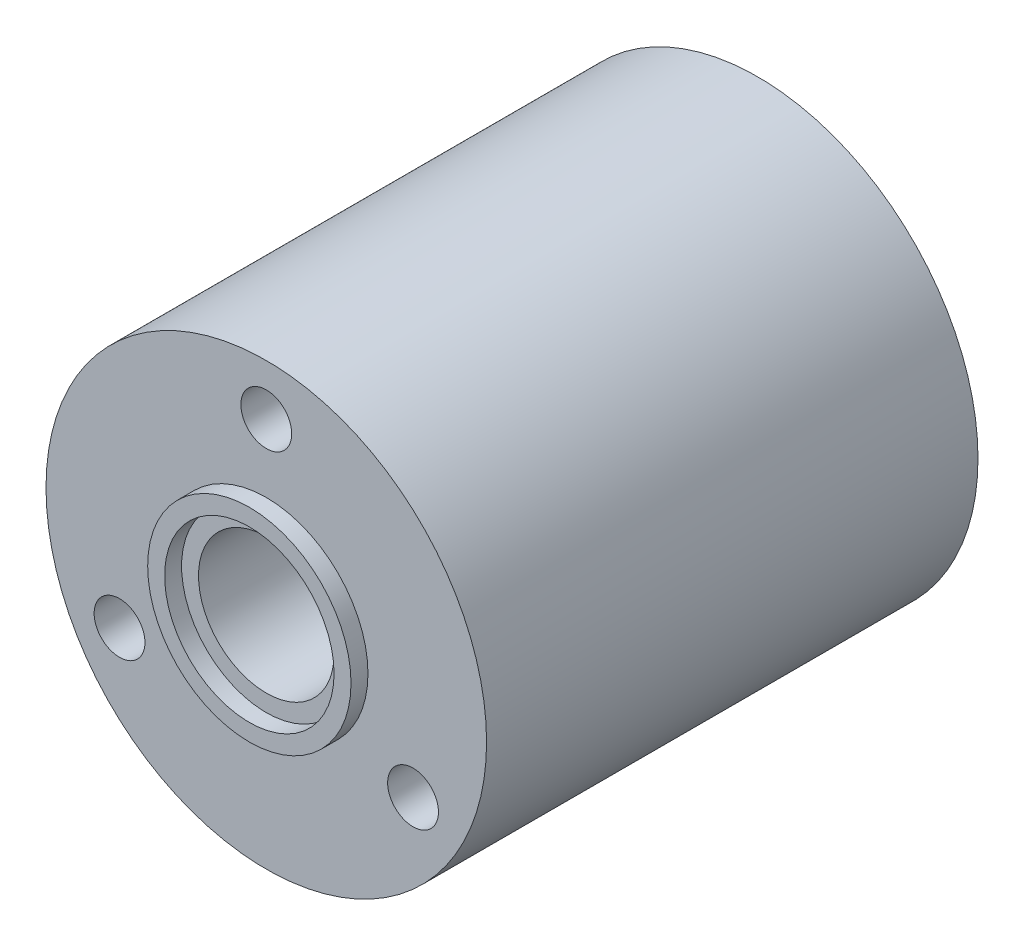
SolidWorks part; units mm, degrees
ref_plane "Front Plane" through (0, 0, 0) normal (0, 0, 1) x (1, 0, 0)
ref_plane "Top Plane" through (0, 0, 0) normal (0, 1, 0) x (1, 0, 0)
ref_plane "Right Plane" through (0, 0, 0) normal (1, 0, 0) x (0, 0, -1)
sketch "Sketch1" plane through (0, 0, 0) normal (0, 0, 1) x (1, 0, 0)
  circle A0 centre (0, 0) radius 5
  circle A1 centre (0, 0) radius 13
  dimension "D1" = 10
  dimension "D2" = 26
extrude "Boss-Extrude1" add sketch "Sketch1" along normal blind 29
sketch "Sketch2" plane through (0, 0, 29) normal (0, 0, 1) x (1, 0, 0)
  circle A0 centre (0, 0) radius 5
  circle A1 centre (0, 0) radius 6
  dimension "D1" = 1
extrude "Boss-Extrude2" add sketch "Sketch2" along normal blind 1
ref_plane "Plane1" through (0, 0, 14.5) normal (0, 0, 1) x (1, 0, 0)
mirror "Mirror1" about plane through (0, 0, 14.5) normal (0, 0, 1) of "Boss-Extrude2"
sketch "Sketch3" plane through (0, 0, 29) normal (0, 0, 1) x (1, 0, 0)
  circle A0 centre (0, 10) radius 1.5
  circle A1 centre (8.6603, -5) radius 1.5
  circle A2 centre (-8.6603, -5) radius 1.5
  point P9 (0, 0)
  dimension "D1" = 3
  dimension "D2" = 10
  dimension "D3" = 3
extrude "Cut-Extrude1" cut sketch "Sketch3" against normal through all
sketch "Sketch4" plane through (0, 0, 29) normal (0, 0, 1) x (1, 0, 0)
  circle A0 centre (0, 0) radius 5
  circle A1 centre (0, 0) radius 4
  dimension "D1" = 10
  dimension "D2" = 8
extrude "Boss-Extrude3" add sketch "Sketch4" against normal blind 29
